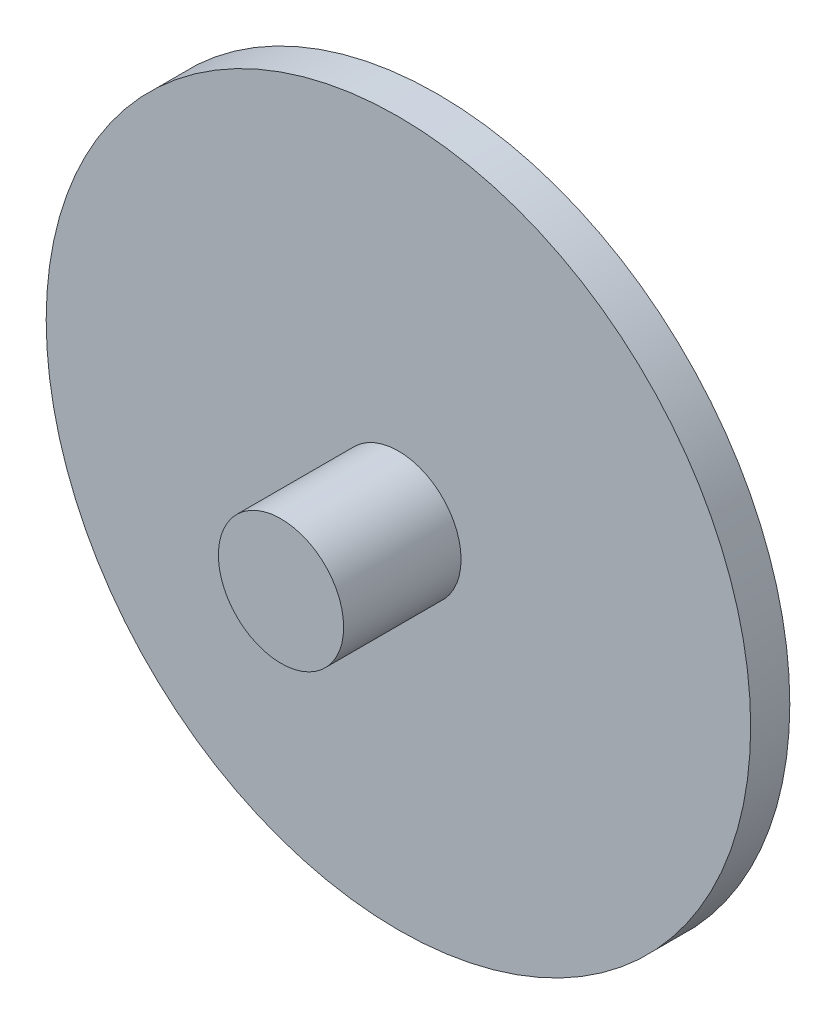
SolidWorks part; units mm, degrees
ref_plane "Front Plane" through (0, 0, 0) normal (0, 0, 1) x (1, 0, 0)
ref_plane "Top Plane" through (0, 0, 0) normal (0, 1, 0) x (1, 0, 0)
ref_plane "Right Plane" through (0, 0, 0) normal (1, 0, 0) x (0, 0, -1)
sketch "Sketch1" plane through (0, 0, 0) normal (0, 0, 1) x (1, 0, 0)
  circle A0 centre (0, 0) radius 8
extrude "Boss-Extrude1" add sketch "Sketch1" along normal blind 20 and the other way blind 15
sketch "Sketch2" plane through (0, 0, 0) normal (0, 0, 1) x (1, 0, 0)
  circle A0 centre (0, 0) radius 45
extrude "Boss-Extrude2" add sketch "Sketch2" along normal blind 5
sketch "Sketch3" plane through (0, 0, 0) normal (0, 0, 1) x (1, 0, 0)
  circle A0 centre (0, 0) radius 2
extrude "Cut-Extrude1" cut sketch "Sketch3" against normal blind 15 and the other way blind 10
